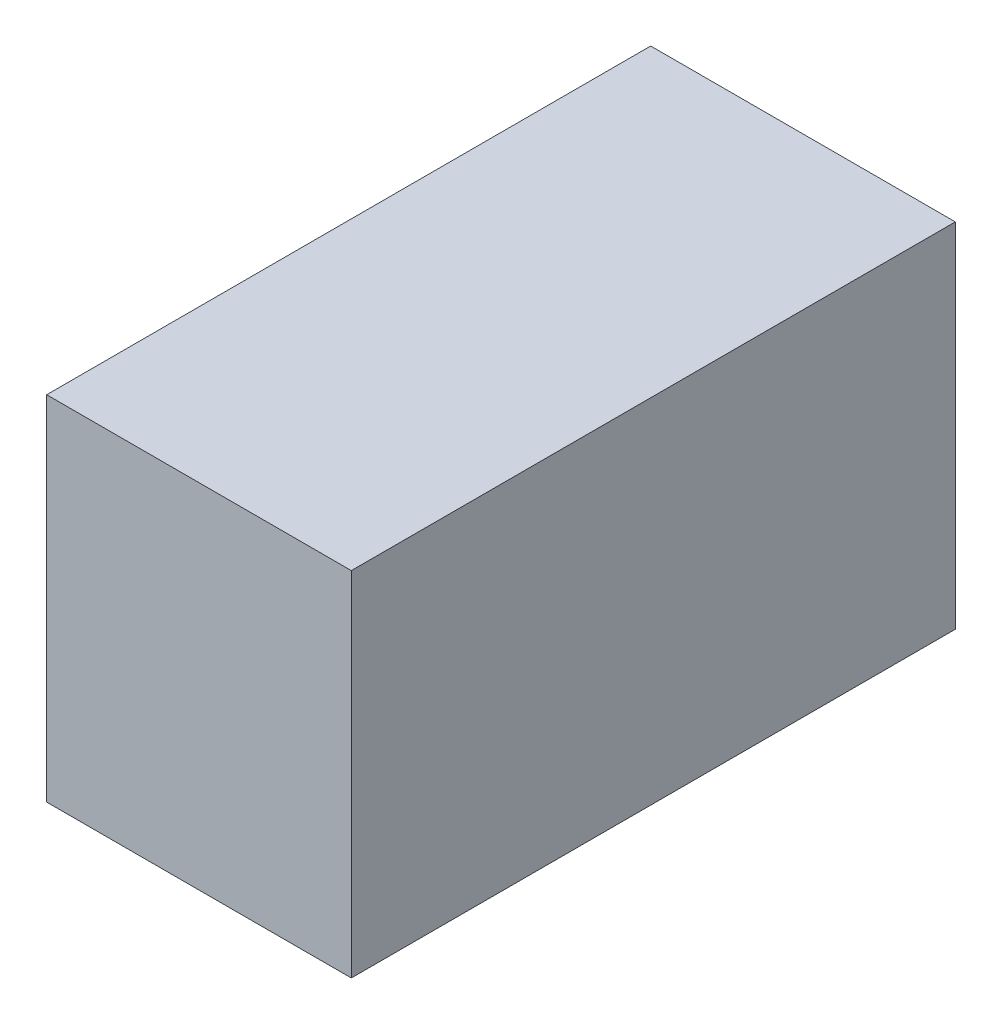
SolidWorks part; units mm, degrees
ref_plane "Front Plane" through (0, 0, 0) normal (0, 0, 1) x (1, 0, 0)
ref_plane "Top Plane" through (0, 0, 0) normal (0, 1, 0) x (1, 0, 0)
ref_plane "Right Plane" through (0, 0, 0) normal (1, 0, 0) x (0, 0, -1)
sketch "Sketch1" plane through (0, 0, 0) normal (0, 0, 1) x (1, 0, 0)
  line L1 (-14.6079, 14.1814) -> (8.5921, 14.1814)
  line L2 (-14.6079, 14.1814) -> (-14.6079, -12.6886)
  line L3 (-14.6079, -12.6886) -> (8.5921, -12.6886)
  line L4 (8.5921, 14.1814) -> (8.5921, -12.6886)
  dimension "D1" = 26.87
  dimension "D2" = 23.2
extrude "Boss-Extrude2" add sketch "Sketch1" along normal blind 46
